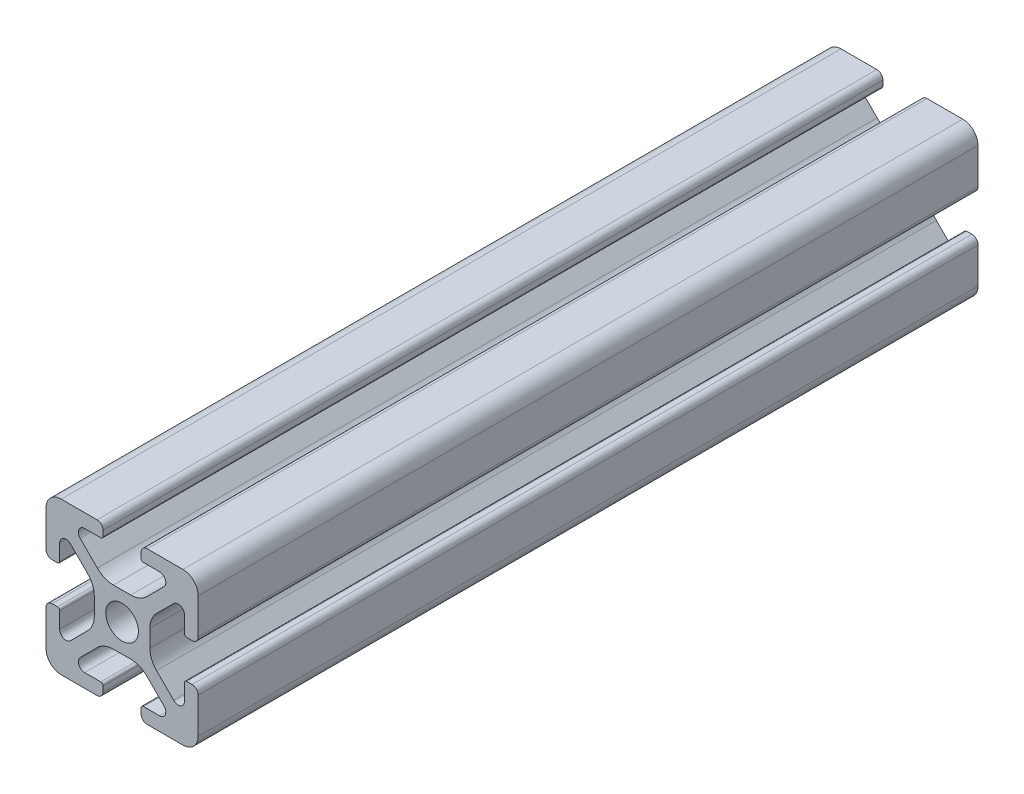
SolidWorks part; units mm, degrees
ref_plane "Ebene vorne" through (0, 0, 0) normal (0, 0, 1) x (1, 0, 0)
ref_plane "Ebene oben" through (0, 0, 0) normal (0, 1, 0) x (1, 0, 0)
ref_plane "Ebene rechts" through (0, 0, 0) normal (1, 0, 0) x (0, 0, -1)
ref_plane "Ebene1" through (0, 0, 100) normal (0, 0, 1) x (1, 0, 0)
sketch "Skizze1" plane through (0, 0, 100) normal (0, 0, 1) x (1, 0, 0)
  line L0 (12.5, 1.5) -> (12.5, 0.8)
  line L1 (13.3, 0) -> (18, 0)
  line L2 (20, 2) -> (20, 6.7)
  line L3 (19.2, 7.5) -> (18.5, 7.5)
  line L4 (18.2, 7.2) -> (18.2, 5.0824)
  line L5 (16.779, 4.4938) -> (14.5287, 6.7441)
  line L6 (13.65, 8.8654) -> (13.65, 11.1346)
  line L7 (14.5287, 13.2559) -> (16.779, 15.5062)
  line L8 (18.2, 14.9176) -> (18.2, 12.8)
  line L9 (18.5, 12.5) -> (19.2, 12.5)
  line L10 (20, 13.3) -> (20, 18)
  line L11 (18, 20) -> (13.3, 20)
  line L12 (12.5, 19.2) -> (12.5, 18.5)
  line L13 (12.8, 18.2) -> (14.9176, 18.2)
  line L14 (15.5062, 16.779) -> (13.2559, 14.5287)
  line L15 (11.1346, 13.65) -> (8.8654, 13.65)
  line L16 (6.7441, 14.5287) -> (4.4938, 16.779)
  line L17 (5.0824, 18.2) -> (7.2, 18.2)
  line L18 (7.5, 18.5) -> (7.5, 19.2)
  line L19 (6.7, 20) -> (2, 20)
  line L20 (0, 18) -> (0, 13.3)
  line L21 (0.8, 12.5) -> (1.5, 12.5)
  line L22 (1.8, 12.8) -> (1.8, 14.9176)
  line L23 (3.221, 15.5062) -> (5.4713, 13.2559)
  line L24 (6.35, 11.1346) -> (6.35, 8.8654)
  line L25 (5.4713, 6.7441) -> (3.221, 4.4938)
  line L26 (1.8, 5.0824) -> (1.8, 7.2)
  line L27 (1.5, 7.5) -> (0.8, 7.5)
  line L28 (0, 6.7) -> (0, 2)
  line L29 (2, 0) -> (6.7, 0)
  line L30 (7.5, 0.8) -> (7.5, 1.5)
  line L31 (7.2, 1.8) -> (5.0824, 1.8)
  line L32 (4.4938, 3.221) -> (6.7441, 5.4713)
  line L33 (8.8654, 6.35) -> (11.1346, 6.35)
  line L34 (13.2559, 5.4713) -> (15.5062, 3.221)
  line L35 (14.9176, 1.8) -> (12.8, 1.8)
  circle A0 centre (10, 10) radius 2.15
  arc A1 (12.8, 1.8) -> (12.5, 1.5) centre (12.8, 1.5) ccw
  arc A2 (12.5, 0.8) -> (13.3, 0) centre (13.3, 0.8) ccw
  arc A3 (18, 0) -> (20, 2) centre (18, 2) ccw
  arc A4 (20, 6.7) -> (19.2, 7.5) centre (19.2, 6.7) ccw
  arc A5 (18.5, 7.5) -> (18.2, 7.2) centre (18.5, 7.2) ccw
  arc A6 (18.2, 5.0824) -> (16.779, 4.4938) centre (17.3676, 5.0824) cw
  arc A7 (14.5287, 6.7441) -> (13.65, 8.8654) centre (16.65, 8.8654) cw
  arc A8 (13.65, 11.1346) -> (14.5287, 13.2559) centre (16.65, 11.1346) cw
  arc A9 (16.779, 15.5062) -> (18.2, 14.9176) centre (17.3676, 14.9176) cw
  arc A10 (18.2, 12.8) -> (18.5, 12.5) centre (18.5, 12.8) ccw
  arc A11 (19.2, 12.5) -> (20, 13.3) centre (19.2, 13.3) ccw
  arc A12 (20, 18) -> (18, 20) centre (18, 18) ccw
  arc A13 (13.3, 20) -> (12.5, 19.2) centre (13.3, 19.2) ccw
  arc A14 (12.5, 18.5) -> (12.8, 18.2) centre (12.8, 18.5) ccw
  arc A15 (14.9176, 18.2) -> (15.5062, 16.779) centre (14.9176, 17.3676) cw
  arc A16 (13.2559, 14.5287) -> (11.1346, 13.65) centre (11.1346, 16.65) cw
  arc A17 (8.8654, 13.65) -> (6.7441, 14.5287) centre (8.8654, 16.65) cw
  arc A18 (4.4938, 16.779) -> (5.0824, 18.2) centre (5.0824, 17.3676) cw
  arc A19 (7.2, 18.2) -> (7.5, 18.5) centre (7.2, 18.5) ccw
  arc A20 (7.5, 19.2) -> (6.7, 20) centre (6.7, 19.2) ccw
  arc A21 (2, 20) -> (0, 18) centre (2, 18) ccw
  arc A22 (0, 13.3) -> (0.8, 12.5) centre (0.8, 13.3) ccw
  arc A23 (1.5, 12.5) -> (1.8, 12.8) centre (1.5, 12.8) ccw
  arc A24 (1.8, 14.9176) -> (3.221, 15.5062) centre (2.6324, 14.9176) cw
  arc A25 (5.4713, 13.2559) -> (6.35, 11.1346) centre (3.35, 11.1346) cw
  arc A26 (6.35, 8.8654) -> (5.4713, 6.7441) centre (3.35, 8.8654) cw
  arc A27 (3.221, 4.4938) -> (1.8, 5.0824) centre (2.6324, 5.0824) cw
  arc A28 (1.8, 7.2) -> (1.5, 7.5) centre (1.5, 7.2) ccw
  arc A29 (0.8, 7.5) -> (0, 6.7) centre (0.8, 6.7) ccw
  arc A30 (0, 2) -> (2, 0) centre (2, 2) ccw
  arc A31 (6.7, 0) -> (7.5, 0.8) centre (6.7, 0.8) ccw
  arc A32 (7.5, 1.5) -> (7.2, 1.8) centre (7.2, 1.5) ccw
  arc A33 (5.0824, 1.8) -> (4.4938, 3.221) centre (5.0824, 2.6324) cw
  arc A34 (6.7441, 5.4713) -> (8.8654, 6.35) centre (8.8654, 3.35) cw
  arc A35 (11.1346, 6.35) -> (13.2559, 5.4713) centre (11.1346, 3.35) cw
  arc A36 (15.5062, 3.221) -> (14.9176, 1.8) centre (14.9176, 2.6324) cw
extrude "Aufsatz-Linear austragen1" add sketch "Skizze1" against normal blind 102.5
